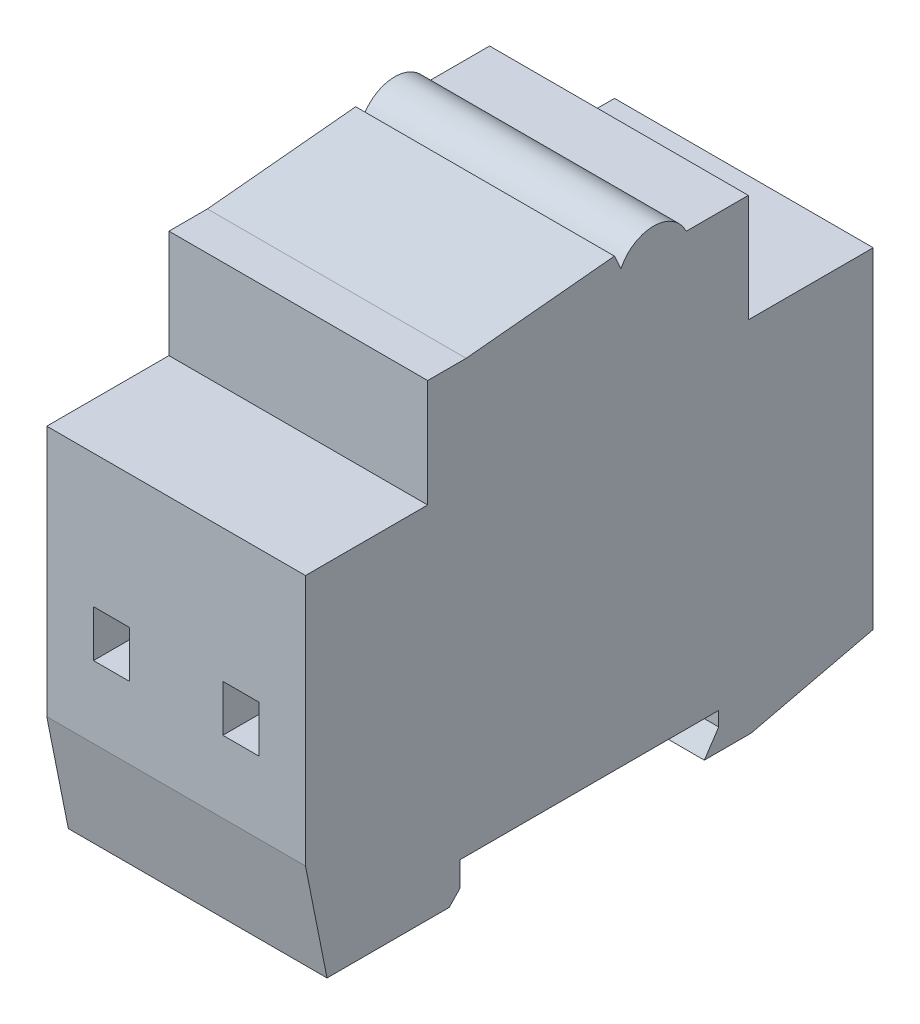
SolidWorks part; units mm, degrees
ref_plane "Спереди" through (0, 0, 0) normal (0, 0, 1) x (1, 0, 0)
ref_plane "Сверху" through (0, 0, 0) normal (0, 1, 0) x (1, 0, 0)
ref_plane "Справа" through (0, 0, 0) normal (1, 0, 0) x (0, 0, -1)
sketch "Эскиз1" plane through (0, 0, 0) normal (1, 0, 0) x (0, 0, -1)
  line L0 (0, 15) -> (3, 0)
  line L1 (3, 0) -> (20, 0)
  line L3 (21.5, 5) -> (21.5, 1.5652)
  line L4 (21.5, 1.5652) -> (20, 0)
  line L5 (21.5, 5) -> (57.5, 5)
  line L6 (57.5, 5) -> (57.5, 3)
  line L7 (57.5, 3) -> (55.5, 0)
  line L8 (55.5, 0) -> (62, 0)
  line L9 (62, 0) -> (79, 4)
  line L10 (79, 4) -> (79, 50)
  line L11 (79, 50) -> (61.6194, 50)
  line L12 (61.6194, 50) -> (61.6194, 65)
  line L13 (61.6194, 65) -> (52.968, 65)
  line L14 (0, 15) -> (0, 50)
  line L15 (0, 50) -> (17, 50)
  line L16 (17, 50) -> (17, 65)
  line L17 (17, 65) -> (22.3559, 65)
  line L18 (22.3559, 65) -> (42.9865, 67)
  line L19 (42.9865, 67) -> (43.8921, 65)
  arc A0 (52.968, 65) -> (43.8921, 65) centre (48.4301, 62.8889) ccw
extrude "Бобышка-Вытянуть1" add sketch "Эскиз1" along normal blind 36
sketch "Эскиз2" plane through (0, 0, -79) normal (0, 0, -1) x (-1, 0, 0)
  line L1 (-29.5, 31.5) -> (-24.5, 31.5)
  line L2 (-29.5, 31.5) -> (-29.5, 25)
  line L3 (-29.5, 25) -> (-24.5, 25)
  line L4 (-24.5, 31.5) -> (-24.5, 25)
  line L5 (-11.5, 31.5) -> (-6.5, 31.5)
  line L6 (-11.5, 31.5) -> (-11.5, 25)
  line L7 (-11.5, 25) -> (-6.5, 25)
  line L8 (-6.5, 31.5) -> (-6.5, 25)
extrude "Вырез-Вытянуть1" cut sketch "Эскиз2" against normal blind 20
sketch "Эскиз3" plane through (0, 0, 0) normal (0, 0, 1) x (1, 0, 0)
  line L1 (6.5, 31.5) -> (11.5, 31.5)
  line L2 (6.5, 31.5) -> (6.5, 25)
  line L3 (6.5, 25) -> (11.5, 25)
  line L4 (11.5, 31.5) -> (11.5, 25)
  line L5 (24.5, 31.5) -> (29.5, 31.5)
  line L6 (24.5, 31.5) -> (24.5, 25)
  line L7 (24.5, 25) -> (29.5, 25)
  line L8 (29.5, 31.5) -> (29.5, 25)
extrude "Вырез-Вытянуть2" cut sketch "Эскиз3" against normal blind 20
